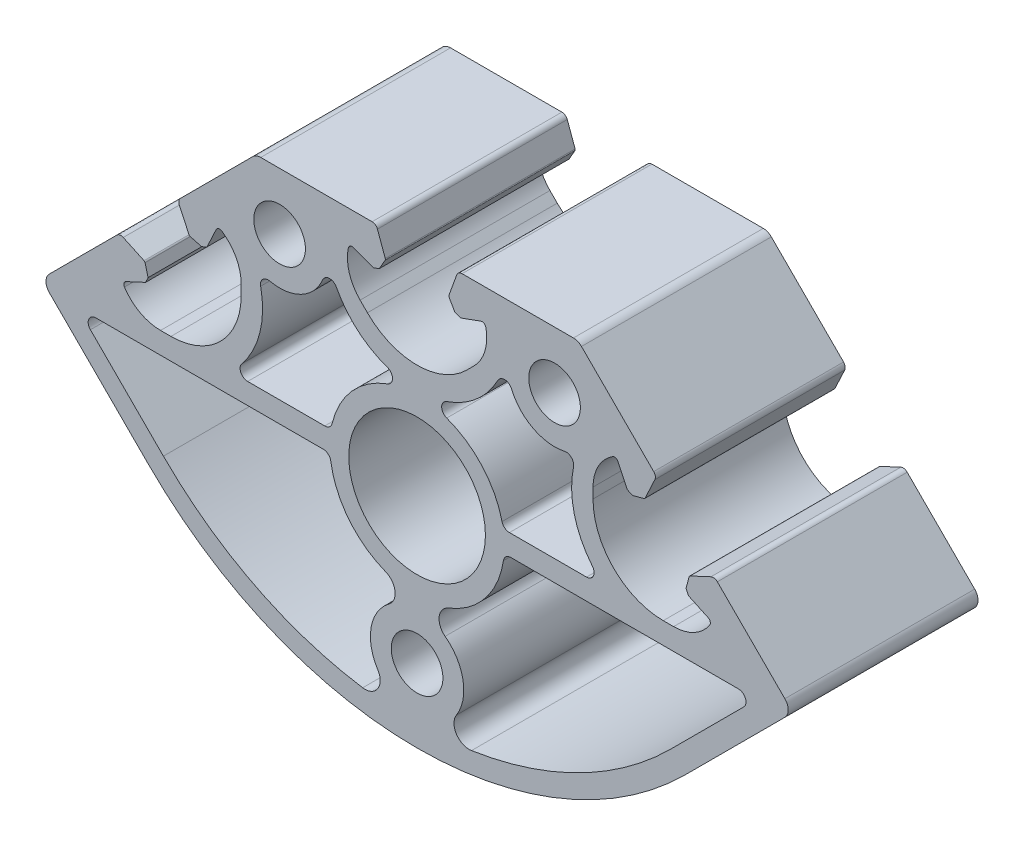
SolidWorks part; units mm, degrees
material "6005-T5"
ref_plane "Front" through (0, 0, 0) normal (0, 0, 1) x (1, 0, 0)
ref_plane "Top" through (0, 0, 0) normal (0, 1, 0) x (1, 0, 0)
ref_plane "Right" through (0, 0, 0) normal (1, 0, 0) x (0, 0, -1)
sketch "Sk Main Extrusion" plane through (0, 0, 0) normal (0, 0, 1) x (1, 0, 0)
  line L52 (-33.4108, -12.1819) -> (-43.0256, -2.5671)
  line L53 (-42.3184, -0.86) -> (-12.3608, -0.86)
  line L54 (43.0256, -2.5671) -> (33.4108, -12.1819)
  line L55 (12.3608, -0.86) -> (42.3184, -0.86)
  line L56 (22.3138, 1.89) -> (12.1613, 1.89)
  line L57 (-12.1613, 1.89) -> (-22.3138, 1.89)
  line L58 (-35.9643, 8.8412) -> (-38.6989, 10.1164)
  line L59 (-39.5462, 9.967) -> (-48.4368, 1.0764)
  line L60 (48.4368, 1.0764) -> (39.5462, 9.967)
  line L61 (38.6989, 10.1164) -> (35.9643, 8.8412)
  line L62 (35.8285, 8.6793) -> (35.4252, 7.1743)
  line L63 (35.4252, 7.1743) -> (35.754, 6.4693)
  line L64 (35.754, 6.4693) -> (38.3365, 5.265)
  line L65 (33.7833, 1.9734) -> (32.4208, 1.9734)
  line L66 (23.1708, 11.2234) -> (23.1708, 12.5859)
  line L67 (26.4625, 17.139) -> (27.6668, 14.5565)
  line L68 (27.6668, 14.5565) -> (28.3718, 14.2278)
  line L69 (28.3718, 14.2278) -> (29.8768, 14.631)
  line L70 (30.0387, 14.7669) -> (31.3138, 17.5015)
  line L71 (5.2221, 27.8065) -> (4.1901, 24.9712)
  line L72 (4.2085, 24.7607) -> (4.9876, 23.4113)
  line L73 (4.9876, 23.4113) -> (5.7185, 23.1453)
  line L74 (5.7185, 23.1453) -> (8.3962, 24.1198)
  line L75 (7.5042, 18.5727) -> (6.5407, 17.6093)
  line L76 (-48.4368, -1.0449) -> (-35.3553, -14.1264)
  line L77 (35.3553, -14.1264) -> (48.4368, -1.0449)
  line L78 (31.1644, 18.3488) -> (21.6525, 27.8607)
  line L79 (20.5919, 28.3) -> (5.9268, 28.3)
  line L80 (-5.9268, 28.3) -> (-20.5919, 28.3)
  line L81 (-21.6525, 27.8607) -> (-31.1644, 18.3488)
  line L82 (-6.5407, 17.6093) -> (-7.5042, 18.5727)
  line L83 (-8.3962, 24.1198) -> (-5.7185, 23.1453)
  line L84 (-5.7185, 23.1453) -> (-4.9876, 23.4113)
  line L85 (-4.9876, 23.4113) -> (-4.2085, 24.7607)
  line L86 (-4.1901, 24.9712) -> (-5.2221, 27.8065)
  line L87 (-31.3138, 17.5015) -> (-30.0387, 14.7669)
  line L88 (-29.8768, 14.631) -> (-28.3718, 14.2278)
  line L89 (-28.3718, 14.2278) -> (-27.6668, 14.5565)
  line L90 (-27.6668, 14.5565) -> (-26.4625, 17.139)
  line L91 (-23.1708, 12.5859) -> (-23.1708, 11.2234)
  line L92 (-32.4208, 1.9734) -> (-33.7833, 1.9734)
  line L93 (-38.3365, 5.265) -> (-35.754, 6.4693)
  line L94 (-35.754, 6.4693) -> (-35.4252, 7.1743)
  line L95 (-35.4252, 7.1743) -> (-35.8285, 8.6793)
  circle A68 centre (0, -19.1) radius 3.4
  circle A69 centre (0, 0) radius 9
  circle A70 centre (18.1066, 20.8) radius 3.4
  circle A71 centre (-18.1066, 20.8) radius 3.4
  arc A72 (-11.372, -1.7112) -> (-12.3608, -0.86) centre (-12.3608, -1.86) ccw
  arc A73 (-11.372, -1.7112) -> (-4.168, -10.7181) centre (0, 0) ccw
  arc A74 (-3.6921, -14.1816) -> (-4.168, -10.7181) centre (-4.8928, -12.5821) ccw
  arc A75 (-3.6921, -14.1816) -> (-5.1778, -22.4186) centre (0, -19.1) ccw
  arc A76 (-7.1649, -25.4747) -> (-5.1778, -22.4186) centre (-6.8616, -23.4978) ccw
  arc A77 (-33.4108, -12.1819) -> (-7.1649, -25.4747) centre (0, 21.2289) ccw
  arc A78 (-42.3184, -0.86) -> (-43.0256, -2.5671) centre (-42.3184, -1.86) ccw
  arc A79 (43.0256, -2.5671) -> (42.3184, -0.86) centre (42.3184, -1.86) ccw
  arc A80 (7.1649, -25.4747) -> (33.4108, -12.1819) centre (0, 21.2289) ccw
  arc A81 (5.1778, -22.4186) -> (7.1649, -25.4747) centre (6.8616, -23.4978) ccw
  arc A82 (-38.6989, 10.1164) -> (-39.5462, 9.967) centre (-39.0159, 9.4366) ccw
  arc A83 (39.5462, 9.967) -> (38.6989, 10.1164) centre (39.0159, 9.4366) ccw
  arc A84 (35.9643, 8.8412) -> (35.8285, 8.6793) centre (36.07, 8.6146) ccw
  arc A85 (38.5427, 4.5368) -> (38.3365, 5.265) centre (38.1252, 4.8119) ccw
  arc A86 (33.7833, 1.9734) -> (38.5427, 4.5368) centre (33.7833, 7.6734) ccw
  arc A87 (23.1708, 11.2234) -> (32.4208, 1.9734) centre (32.4208, 11.2234) ccw
  arc A88 (25.7342, 17.3452) -> (23.1708, 12.5859) centre (28.8708, 12.5859) ccw
  arc A89 (26.4625, 17.139) -> (25.7342, 17.3452) centre (26.0094, 16.9277) ccw
  arc A90 (29.8768, 14.631) -> (30.0387, 14.7669) centre (29.8121, 14.8725) ccw
  arc A91 (31.3138, 17.5015) -> (31.1644, 18.3488) centre (30.6341, 17.8184) ccw
  arc A92 (5.9268, 28.3) -> (5.2221, 27.8065) centre (5.9268, 27.55) ccw
  arc A93 (4.1901, 24.9712) -> (4.2085, 24.7607) centre (4.425, 24.8857) ccw
  arc A94 (9.057, 23.7507) -> (8.3962, 24.1198) centre (8.5672, 23.65) ccw
  arc A95 (-48.4368, 1.0764) -> (-48.4368, -1.0449) centre (-47.3762, 0.0157) ccw
  arc A96 (-35.3553, -14.1264) -> (35.3553, -14.1264) centre (0, 21.2289) ccw
  arc A97 (48.4368, -1.0449) -> (48.4368, 1.0764) centre (47.3762, 0.0157) ccw
  arc A98 (21.6525, 27.8607) -> (20.5919, 28.3) centre (20.5919, 26.8) ccw
  arc A99 (-20.5919, 28.3) -> (-21.6525, 27.8607) centre (-20.5919, 26.8) ccw
  arc A100 (5.1778, -22.4186) -> (3.6921, -14.1816) centre (0, -19.1) ccw
  arc A101 (4.168, -10.7181) -> (3.6921, -14.1816) centre (4.8928, -12.5821) ccw
  arc A102 (4.168, -10.7181) -> (11.372, -1.7112) centre (0, 0) ccw
  arc A103 (12.3608, -0.86) -> (11.372, -1.7112) centre (12.3608, -1.86) ccw
  arc A104 (12.4396, 18.4109) -> (10.6322, 18.4861) centre (11.5182, 18.0224) ccw
  arc A105 (12.4396, 18.4109) -> (19.4129, 14.7903) centre (18.1066, 20.8) ccw
  arc A106 (20.6041, 13.6085) -> (19.4129, 14.7903) centre (19.6253, 13.8132) ccw
  arc A107 (20.6041, 13.6085) -> (23.0858, 3.5256) centre (32.3501, 11.1527) ccw
  arc A108 (22.3138, 1.89) -> (23.0858, 3.5256) centre (22.3138, 2.89) ccw
  arc A109 (11.1884, 2.6588) -> (12.1613, 1.89) centre (12.1613, 2.89) ccw
  arc A110 (11.1884, 2.6588) -> (3.8983, 10.8191) centre (0, 0) ccw
  arc A111 (3.9113, 12.7053) -> (3.8983, 10.8191) centre (4.2372, 11.7599) ccw
  arc A112 (3.9113, 12.7053) -> (10.6322, 18.4861) centre (0, 24.05) ccw
  arc A113 (-10.6322, 18.4861) -> (-12.4396, 18.4109) centre (-11.5182, 18.0224) ccw
  arc A114 (-10.6322, 18.4861) -> (-3.9113, 12.7053) centre (0, 24.05) ccw
  arc A115 (-3.8983, 10.8191) -> (-3.9113, 12.7053) centre (-4.2372, 11.7599) ccw
  arc A116 (-3.8983, 10.8191) -> (-11.1884, 2.6588) centre (0, 0) ccw
  arc A117 (-12.1613, 1.89) -> (-11.1884, 2.6588) centre (-12.1613, 2.89) ccw
  arc A118 (-23.0858, 3.5256) -> (-22.3138, 1.89) centre (-22.3138, 2.89) ccw
  arc A119 (-23.0858, 3.5256) -> (-20.6041, 13.6085) centre (-32.3501, 11.1527) ccw
  arc A120 (-19.4129, 14.7903) -> (-20.6041, 13.6085) centre (-19.6253, 13.8132) ccw
  arc A121 (-19.4129, 14.7903) -> (-12.4396, 18.4109) centre (-18.1066, 20.8) ccw
  arc A122 (7.5042, 18.5727) -> (9.057, 23.7507) centre (3.4737, 22.6032) ccw
  arc A123 (-6.5407, 17.6093) -> (6.5407, 17.6093) centre (0, 24.15) ccw
  arc A124 (-9.057, 23.7507) -> (-7.5042, 18.5727) centre (-3.4737, 22.6032) ccw
  arc A125 (-8.3962, 24.1198) -> (-9.057, 23.7507) centre (-8.5672, 23.65) ccw
  arc A126 (-4.2085, 24.7607) -> (-4.1901, 24.9712) centre (-4.425, 24.8857) ccw
  arc A127 (-5.2221, 27.8065) -> (-5.9268, 28.3) centre (-5.9268, 27.55) ccw
  arc A128 (-31.1644, 18.3488) -> (-31.3138, 17.5015) centre (-30.6341, 17.8184) ccw
  arc A129 (-30.0387, 14.7669) -> (-29.8768, 14.631) centre (-29.8121, 14.8725) ccw
  arc A130 (-25.7342, 17.3452) -> (-26.4625, 17.139) centre (-26.0094, 16.9277) ccw
  arc A131 (-23.1708, 12.5859) -> (-25.7342, 17.3452) centre (-28.8708, 12.5859) ccw
  arc A132 (-32.4208, 1.9734) -> (-23.1708, 11.2234) centre (-32.4208, 11.2234) ccw
  arc A133 (-38.5427, 4.5368) -> (-33.7833, 1.9734) centre (-33.7833, 7.6734) ccw
  arc A134 (-38.3365, 5.265) -> (-38.5427, 4.5368) centre (-38.1252, 4.8119) ccw
  arc A135 (-35.8285, 8.6793) -> (-35.9643, 8.8412) centre (-36.07, 8.6146) ccw
extrude "Main Extrusion" add sketch "Sk Main Extrusion" against normal blind 25
sketch "Threaded Insert Mate Sketch" plane through (0, 0, 0) normal (0, 0, 1) x (1, 0, 0)
  line L1 (-30.0381, 9.1513) -> (-35.2, 14.3132) construction
  line L2 (-43.9915, 5.5217) -> (-26.4085, 23.1047) construction
  line L5 (0, -9) -> (0, 9) construction
  line L6 (20.5919, 28.3) -> (5.9268, 28.3) construction
  line L7 (-21.6525, 27.8607) -> (-31.1644, 18.3488) construction
  line L8 (-39.5462, 9.967) -> (-48.4368, 1.0764) construction
  circle A0 centre (0, 21) radius 5.6515
  circle A1 centre (-30.0381, 9.1513) radius 5.6515
  circle A2 centre (0, 0) radius 9 construction
  circle A4 centre (30.0381, 9.1513) radius 5.6515
  point P15 (-35.2, 14.3132)
equation "\"Weight kg\"= round ( \"SW-Mass\" , 2 )"
equation "\"Weight lbs\"= round ( \"SW-Mass\" * 2.2046 , 2 )"
equation "\"Length mm\"= round ( \"Length@Main Extrusion\" , 2 )"
equation "\"Length in\"= round ( \"Length@Main Extrusion\" / 25.4 , 3 )"
equation "\"D3@Threaded Insert Mate Sketch\"=\"D2@Threaded Insert Mate Sketch\""
equation "\"D4@Threaded Insert Mate Sketch\"=\"D1@Threaded Insert Mate Sketch\""
